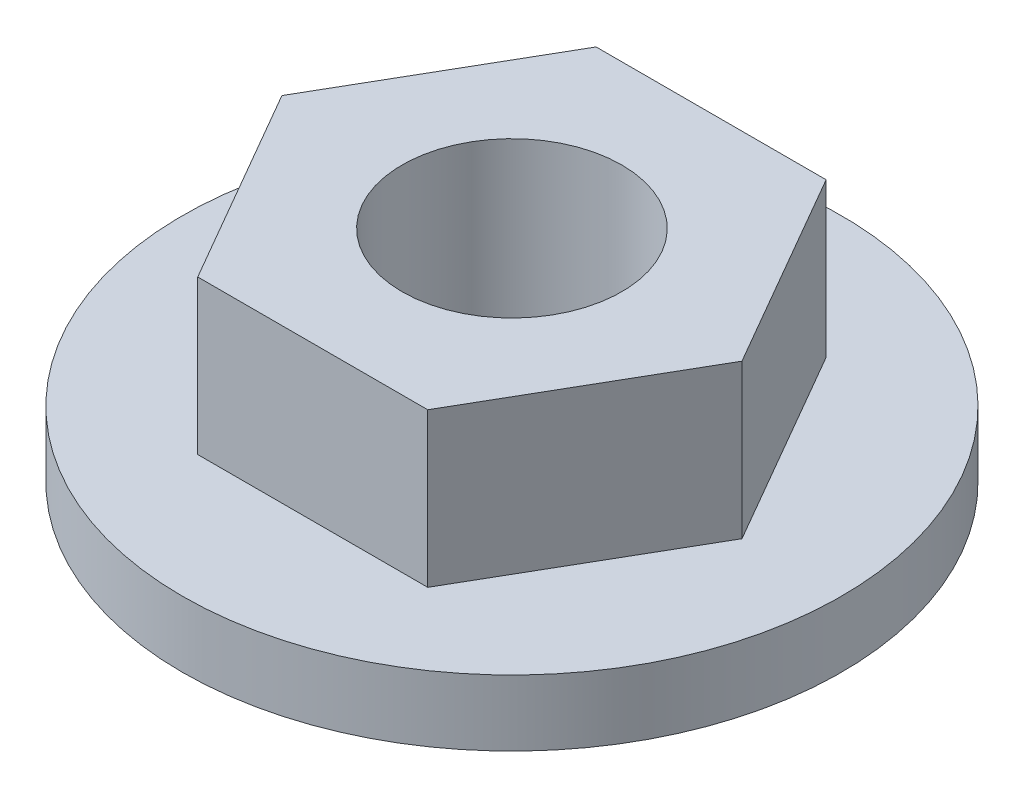
SolidWorks part; units mm, degrees
ref_plane "Front Plane" through (0, 0, 0) normal (0, 0, 1) x (1, 0, 0)
ref_plane "Top Plane" through (0, 0, 0) normal (0, 1, 0) x (1, 0, 0)
ref_plane "Right Plane" through (0, 0, 0) normal (1, 0, 0) x (0, 0, -1)
sketch "Sketch3" plane through (0, 0, 0) normal (0, 1, 0) x (1, 0, 0)
  circle A0 centre (0, 0) radius 3.175
  circle A1 centre (0, 0) radius 9.525
  dimension "D1" = 6.35
  dimension "D2" = 19.05
extrude "Boss-Extrude1" add sketch "Sketch3" along normal blind 1.905
sketch "Sketch4" plane through (0, 1.905, 0) normal (0, 1, 0) x (1, 0, 0)
  line L1 (6.6476, 0) -> (3.3238, 5.757)
  line L2 (3.3238, 5.757) -> (-3.3238, 5.757)
  line L3 (-3.3238, 5.757) -> (-6.6476, 0)
  line L4 (-6.6476, 0) -> (-3.3238, -5.757)
  line L5 (-3.3238, -5.757) -> (3.3238, -5.757)
  line L6 (3.3238, -5.757) -> (6.6476, 0)
  circle A0 centre (0, 0) radius 3.175
  circle A2 centre (0, 0) radius 5.757 construction
  dimension "D1" = 6.35
extrude "Boss-Extrude2" add sketch "Sketch4" along normal blind 4.445
